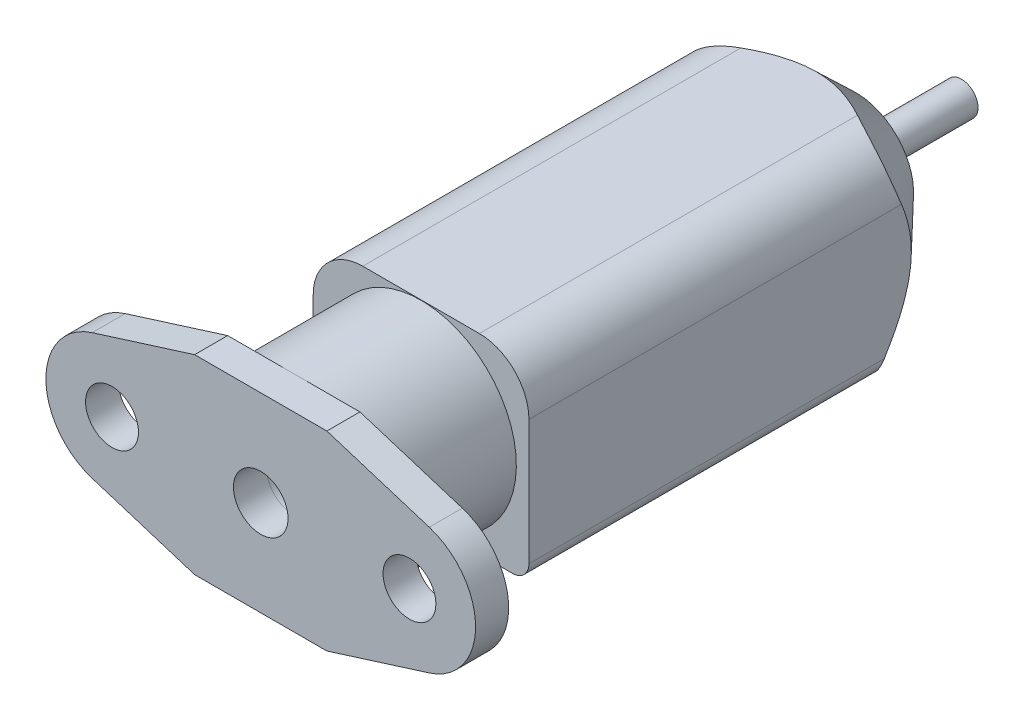
SolidWorks part; units mm, degrees
ref_plane "Alzado" through (0, 0, 0) normal (0, 0, 1) x (1, 0, 0)
ref_plane "Planta" through (0, 0, 0) normal (0, 1, 0) x (1, 0, 0)
ref_plane "Vista lateral" through (0, 0, 0) normal (1, 0, 0) x (0, 0, -1)
sketch "Croquis1" plane through (0, 0, 0) normal (0, 0, 1) x (1, 0, 0)
  line L0 (4, 5.763) -> (10.196, 3.8191)
  line L1 (-4, 5.763) -> (-10.1991, 3.8155)
  line L2 (-4, -5.765) -> (-10.1991, -3.8177)
  line L3 (4, -5.765) -> (10.1978, -3.8173)
  line L4 (4, -5.765) -> (-4, -5.765)
  line L5 (-4, 5.763) -> (4, 5.763)
  circle A0 centre (8.998, 0.0006) radius 1.5982
  circle A1 centre (-9.0001, -0.0011) radius 1.601
  circle A2 centre (0, 0) radius 1.6509
  arc A3 (10.1978, -3.8173) -> (10.196, 3.8191) centre (8.998, 0.0006) ccw
  arc A4 (-10.1991, 3.8155) -> (-10.1991, -3.8177) centre (-9.0001, -0.0011) ccw
extrude "Saliente-Extruir7" add sketch "Croquis1" against normal blind 2 separate body
sketch "Croquis2" plane through (0, 0, -2) normal (0, 0, -1) x (-1, 0, 0)
  circle A0 centre (0, 0) radius 5.765
  circle A1 centre (0, 0) radius 1.6512
extrude "Saliente-Extruir8" add sketch "Croquis2" along normal blind 7.7
sketch "Croquis3" plane through (0, 0, -9.7) normal (0, 0, -1) x (-1, 0, 0)
  line L1 (3.5269, 5.7838) -> (-3.5269, 5.7838)
  line L2 (6.5269, 2.7838) -> (6.5269, -4.7838)
  line L3 (5.5269, -5.7838) -> (-5.5269, -5.7838)
  line L4 (-6.5269, 2.7838) -> (-6.5269, -4.7838)
  line L5 (6.5269, 5.7838) -> (-6.5269, -5.7838) construction
  line L6 (6.5269, -5.7838) -> (-6.5269, 5.7838) construction
  arc A0 (-3.5269, 5.7838) -> (-6.5269, 2.7838) centre (-3.5269, 2.7838) ccw
  arc A1 (3.5269, 5.7838) -> (6.5269, 2.7838) centre (3.5269, 2.7838) cw
  arc A2 (-5.5269, -5.7838) -> (-6.5269, -4.7838) centre (-5.5269, -4.7838) cw
  arc A3 (6.5269, -4.7838) -> (5.5269, -5.7838) centre (5.5269, -4.7838) cw
  point P0 (0, 0)
  dimension "D1" = 3
  dimension "D2" = 1
extrude "Saliente-Extruir9" add sketch "Croquis3" along normal blind 26.3
ref_plane "Plano1" through (0, 5.765, 0) normal (0, 1, 0) x (1, 0, 0)
ref_axis "Eje1" through (0, 0, -39.9199) along (0, 0, 1)
sketch "Croquis5" plane through (0, 0, 0) normal (0, 1, 0) x (1, 0, 0)
  line L0 (0, 36) -> (-3.5, 36) construction
  line L1 (-3.5269, 36) -> (3.5269, 36) construction
  line L2 (-3.5, 36) -> (-8.4726, 30.8035)
  line L3 (-3.5, 36) -> (-8.4726, 36)
  line L4 (-8.4726, 30.8035) -> (-8.4726, 36)
revolve "Cortar-Revolución1" cut sketch "Croquis5" angle 360 about axis through (0, 0, -39.9199) along (0, 0, 1)
sketch "Croquis6" plane through (0, 0, -36) normal (0, 0, -1) x (-1, 0, 0)
  circle A0 centre (0, 0) radius 0.9994
extrude "Saliente-Extruir10" add sketch "Croquis6" along normal blind 6.4
